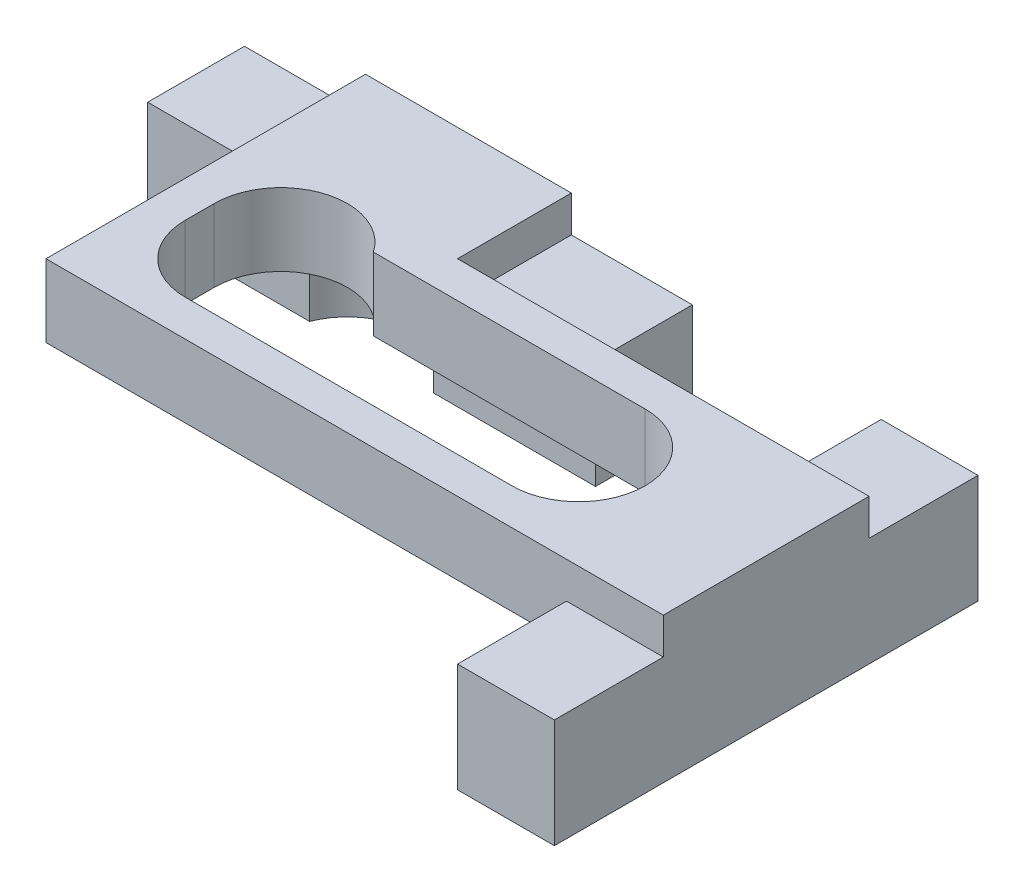
SolidWorks part; units mm, degrees
ref_plane "Plano frontal" through (0, 0, 0) normal (0, 0, 1) x (1, 0, 0)
ref_plane "Plano superior" through (0, 0, 0) normal (0, 1, 0) x (1, 0, 0)
ref_plane "Plano direito" through (0, 0, 0) normal (1, 0, 0) x (0, 0, -1)
sketch "Esboço1" plane through (0, 0, 0) normal (0, 0, 1) x (1, 0, 0)
  line L0 (0, -2.3667) -> (0, 5.2111) construction
  line L1 (9.25, 0) -> (-9.25, 0)
  line L2 (-9.25, 0) -> (-9.25, 3)
  line L3 (-9.25, 3) -> (-4.25, 3)
  line L4 (-4.25, 3) -> (-4.25, 6)
  line L5 (-4.25, 6) -> (4.25, 6)
  line L6 (9.25, 0) -> (9.25, 3)
  line L7 (9.25, 3) -> (4.25, 3)
  line L8 (4.25, 3) -> (4.25, 6)
  point P9 (0, 0)
  point P13 (0, 6)
  dimension "D1" = 5
  dimension "D2" = 8.5
  dimension "D3" = 3
  dimension "D4" = 3
extrude "Ressalto-extrusão1" add sketch "Esboço1" along normal blind 4
sketch "Esboço3" plane through (0, 0, 4) normal (0, 0, 1) x (1, 0, 0)
  line L1 (-4.25, 6) -> (4.25, 6)
  line L2 (-4.25, 6) -> (-4.25, 3)
  line L3 (-4.25, 3) -> (4.25, 3)
  line L4 (4.25, 6) -> (4.25, 3)
extrude "Ressalto-extrusão2" add sketch "Esboço3" along normal blind 9.2
sketch "Esboço4" plane through (4.25, 0, 0) normal (1, 0, 0) x (0, 0, -1)
  line L0 (-13.2, 3) -> (-4, 3) construction
  line L1 (-13.2, 6) -> (-4.7, 6)
  line L2 (-13.2, 6) -> (-13.2, 3)
  line L3 (-13.2, 3) -> (-4.7, 3)
  line L4 (-4.7, 6) -> (-4.7, 3)
  dimension "D1" = 8.5
extrude "Ressalto-extrusão3" add sketch "Esboço4" along normal blind 13
sketch "Esboço5" plane through (17.25, 0, 0) normal (1, 0, 0) x (0, 0, -1)
  line L0 (-8.95, -1.8473) -> (-8.95, 10.6863) construction
  line L2 (-17.7, 0) -> (-17.7, 4.5)
  line L3 (-17.7, 4.5) -> (-13.2, 4.5)
  line L4 (-13.2, 4.5) -> (-13.2, 6)
  line L6 (-17.7, 0) -> (-0.2, 0)
  line L11 (-13.2, 6) -> (-4.7, 6)
  line L12 (-4.7, 6) -> (-13.2, 6) construction
  line L14 (-0.2, 0) -> (-0.2, 4.5)
  line L15 (-0.2, 4.5) -> (-4.7, 4.5)
  line L16 (-4.7, 4.5) -> (-4.7, 6)
  point P4 (-8.95, 0)
  point P13 (-8.95, 0)
  point P16 (-8.95, 6)
  dimension "D1" = 4.5
  dimension "D2" = 4.5
extrude "Ressalto-extrusão6" add sketch "Esboço5" along normal blind 4
sketch "Esboço8" plane through (0, 6, 0) normal (0, 1, 0) x (1, 0, 0)
  line L0 (0, 3.2032) -> (0, -19.2438) construction
  line L1 (25.2074, -8.95) -> (-8.7102, -8.95) construction
  line L9 (-4.25, -4) -> (-9.25, -4) construction
  line L10 (13.5, -6.2) -> (2.2716, -6.2)
  line L11 (13.5, -11.7) -> (0, -11.7)
  line L13 (17.25, -13.2) -> (17.25, -17.7) construction
  line L14 (-2.75, -7.75) -> (-2.75, -8.95)
  arc A3 (2.2716, -6.2) -> (-2.75, -7.75) centre (0, -7.75) ccw
  arc A4 (13.5, -11.7) -> (13.5, -6.2) centre (13.5, -8.95) ccw
  arc A5 (0, -11.7) -> (-2.75, -8.95) centre (0, -8.95) cw
  point P16 (0, -7.75)
  point P20 (0, -8.95)
  dimension "D1" = 5.5
  dimension "D3" = 3.75
  dimension "D2" = 3.75
extrude "Corte-extrusão3" cut sketch "Esboço8" against normal through all
sketch "Esboço9" plane through (0, 3, 0) normal (0, 1, 0) x (1, 0, 0)
  line L1 (-9.25, 0) -> (-4.25, 0)
  line L2 (-9.25, 0) -> (-9.25, -4)
  line L3 (-9.25, -4) -> (-4.25, -4)
  line L4 (-4.25, 0) -> (-4.25, -4)
  line L5 (4.25, 0) -> (9.25, 0)
  line L6 (4.25, 0) -> (4.25, -4)
  line L7 (4.25, -4) -> (9.25, -4)
  line L8 (9.25, 0) -> (9.25, -4)
extrude "Ressalto-extrusão7" add sketch "Esboço9" along normal blind 1.5
sketch "Esboço10" plane through (0, 0, 0) normal (0, -1, 0) x (1, 0, 0)
  line L0 (0, -2.4914) -> (0, 17.4355) construction
  line L1 (-9.25, 4) -> (9.25, 4) construction
  line L2 (29.432, 8.95) -> (12.4837, 8.95) construction
  line L3 (17.25, 17.7) -> (17.25, 0.2) construction
  circle A0 centre (0, 5) radius 2.75
  circle A1 centre (16.25, 8.95) radius 2.75
  dimension "D1" = 5.5
  dimension "D2" = 1
  dimension "D3" = 1
extrude "Corte-extrusão4" cut sketch "Esboço10" against normal blind 3
